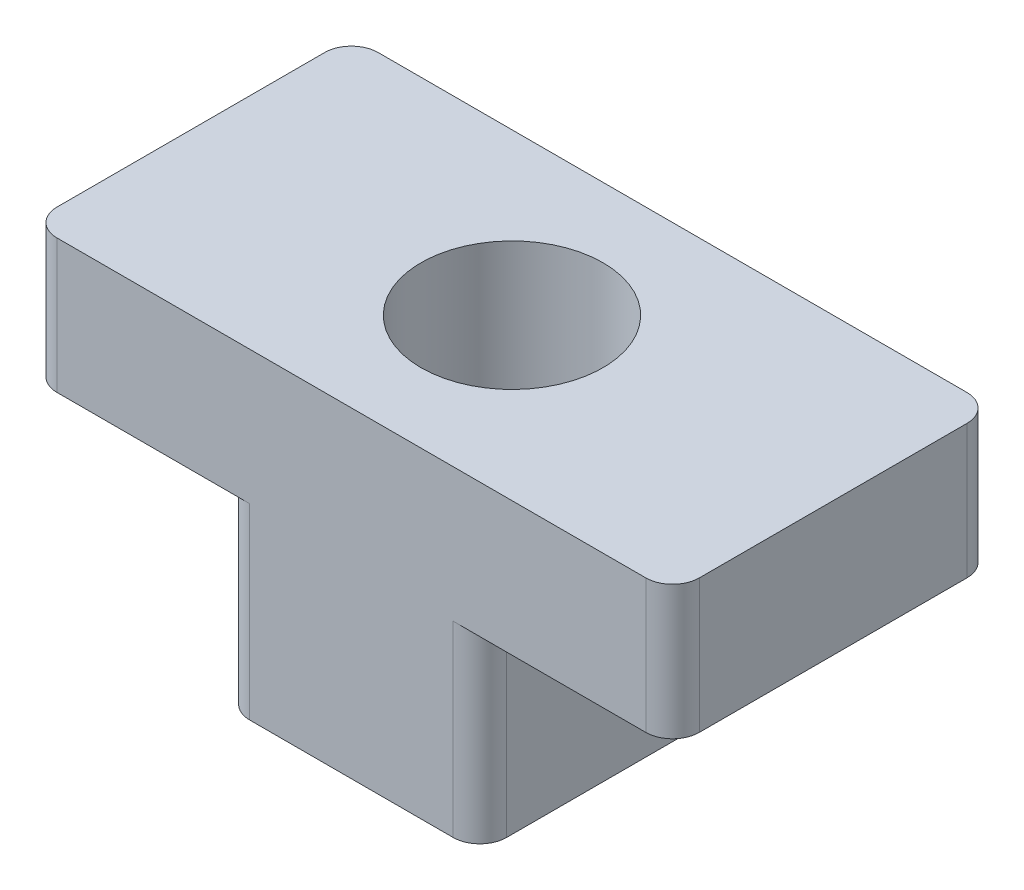
SolidWorks part; units mm, degrees
ref_plane "Plan de face" through (0, 0, 0) normal (0, 0, 1) x (1, 0, 0)
ref_plane "Plan de dessus" through (0, 0, 0) normal (0, 1, 0) x (1, 0, 0)
ref_plane "Plan de droite" through (0, 0, 0) normal (1, 0, 0) x (0, 0, -1)
sketch "Esquisse1" plane through (0, 0, 0) normal (0, 0, 1) x (1, 0, 0)
  line L0 (-6, 0) -> (-2.4, 0)
  line L1 (-2.4, -3.5) -> (2.4, -3.5)
  line L2 (-6, 0) -> (-6, 2.5)
  line L3 (-6, 2.5) -> (6, 2.5)
  line L4 (6, 0) -> (6, 2.5)
  line L5 (-6, 0) -> (6, 0) construction
  line L7 (-2.4, 0) -> (-2.4, -3.5)
  line L8 (6, 0) -> (2.4, 0)
  line L9 (2.4, 0) -> (2.4, -3.5)
  point P0 (0, 0)
  dimension "D1" = 12
  dimension "D2" = 4.8
  dimension "D3" = 2.5
  dimension "D4" = 3.5
extrude "Boss.-Extru.1" add sketch "Esquisse1" along normal mid plane 6
sketch "Esquisse2" plane through (0, 2.5, 0) normal (0, 1, 0) x (1, 0, 0)
  circle A0 centre (0, 0) radius 1.7
  dimension "D1" = 3.4
extrude "Enlèv. mat.-Extru.1" cut sketch "Esquisse2" against normal through all
fillet "Congé2" radius 0.5 8 edges at (-6, 1.25, -3) (-2.4, -1.75, -3) (2.4, -1.75, -3) (6, 1.25, -3) (2.4, -1.75, 3) (-2.4, -1.75, 3) (-6, 1.25, 3) (6, 1.25, 3)
sketch "Esquisse3" plane through (0, 0, 0) normal (0, -1, 0) x (1, 0, 0)
  line L0 (2.4, 2.5) -> (2.4, -2.5) construction
  line L1 (-2.4, -1.7) -> (2.4, -1.7)
  line L2 (-2.4, -1.7) -> (-2.4, 1.7)
  line L3 (-2.4, 1.7) -> (2.4, 1.7)
  line L4 (2.4, -1.7) -> (2.4, 1.7)
  line L5 (-2.4, -1.7) -> (2.4, 1.7) construction
  line L6 (-2.4, 1.7) -> (2.4, -1.7) construction
  circle A0 centre (0, 0) radius 1.7 construction
  point P0 (0, 0)
